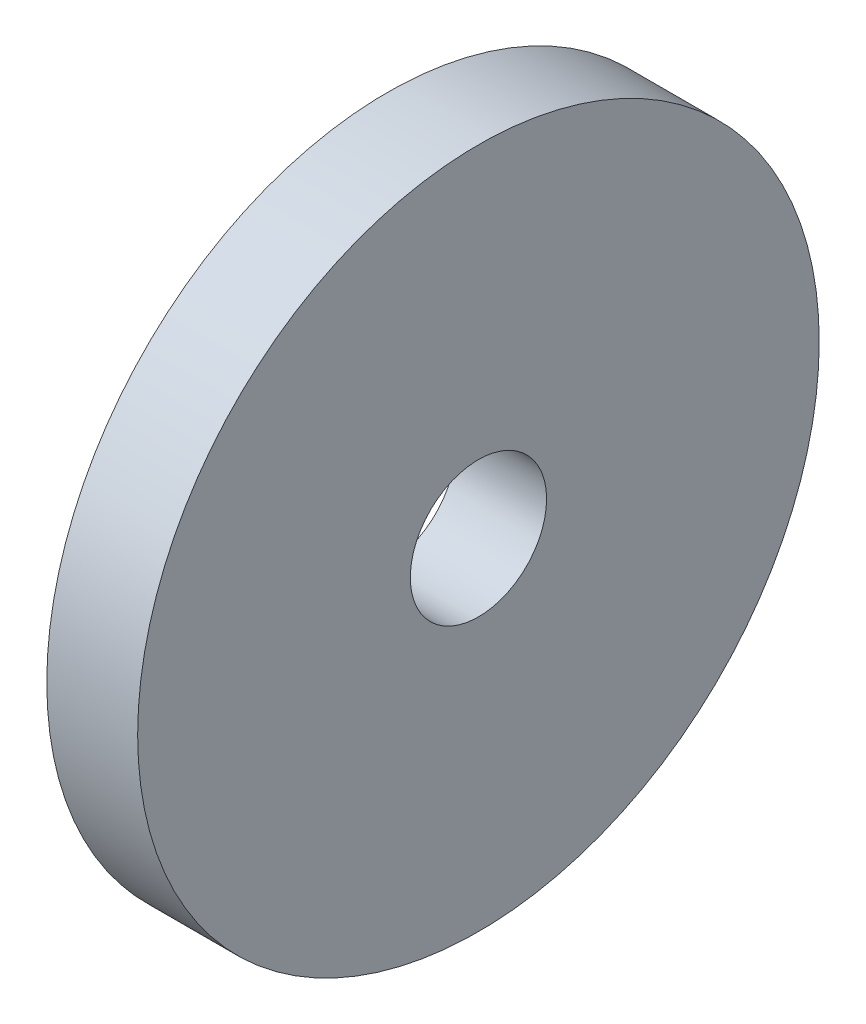
SolidWorks part; units mm, degrees
material "Pine"
ref_plane "Front Plane" through (0, 0, 0) normal (0, 0, 1) x (1, 0, 0)
ref_plane "Top Plane" through (0, 0, 0) normal (0, 1, 0) x (1, 0, 0)
ref_plane "Right Plane" through (0, 0, 0) normal (1, 0, 0) x (0, 0, -1)
sketch "Sketch1" plane through (0, 0, 0) normal (1, 0, 0) x (0, 0, -1)
  circle A0 centre (0, 0) radius 7.5
  dimension "D1" = 15
extrude "Boss-Extrude1" add sketch "Sketch1" along normal blind 2
sketch "Sketch2" plane through (2, 0, 0) normal (1, 0, 0) x (0, 0, -1)
  circle A0 centre (0, 0) radius 1.5
extrude "Cut-Extrude1" cut sketch "Sketch2" against normal through all
